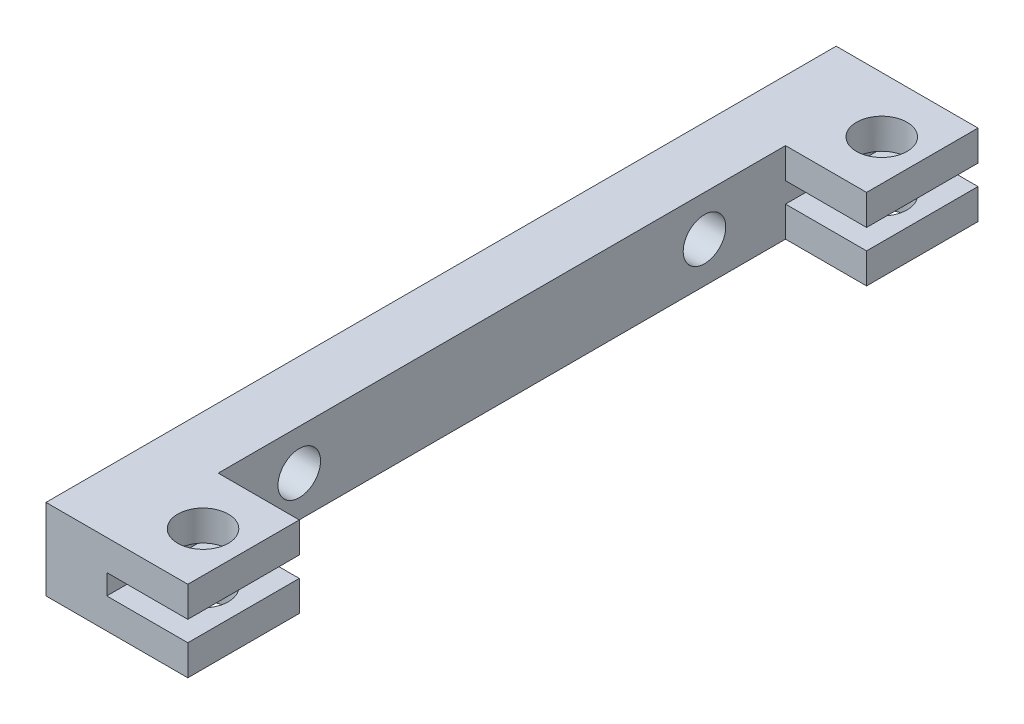
SolidWorks part; units mm, degrees
ref_plane "前视基准面" through (0, 0, 0) normal (0, 0, 1) x (1, 0, 0)
ref_plane "上视基准面" through (0, 0, 0) normal (0, 1, 0) x (1, 0, 0)
ref_plane "右视基准面" through (0, 0, 0) normal (1, 0, 0) x (0, 0, -1)
sketch "草图1" plane through (0, 0, 0) normal (0, 0, 1) x (1, 0, 0)
  line L0 (-5441.3907, 1449.7886) -> (-5441.3907, 1457.7886)
  line L1 (-5427.3907, 1457.7886) -> (-5427.3907, 1454.7886)
  line L2 (-5435.3907, 1454.7886) -> (-5435.3907, 1452.7886)
  line L3 (-5427.3907, 1452.7886) -> (-5427.3907, 1449.7886)
  line L4 (-5427.3907, 1449.7886) -> (-5441.3907, 1449.7886)
  line L5 (-5435.3907, 1454.7886) -> (-5427.3907, 1454.7886)
  line L6 (-5435.3907, 1452.7886) -> (-5427.3907, 1452.7886)
  line L7 (-5427.3907, 1457.7886) -> (-5441.3907, 1457.7886)
  line L20 (-5427.3907, 1453.7886) -> (-5441.3907, 1453.7886) construction
extrude "凸台-拉伸1" add sketch "草图1" along normal blind 78
sketch "草图2" plane through (0, 1457.7886, 0) normal (0, 1, 0) x (1, 0, 0)
  line L0 (-5441.3907, -39) -> (-5427.3907, -39) construction
  line L1 (-5441.3907, -78) -> (-5441.3907, 0) construction
  line L2 (-5427.3907, -78) -> (-5427.3907, 0) construction
  line L4 (-5427.3907, -67) -> (-5435.3907, -67)
  line L5 (-5427.3907, -67) -> (-5427.3907, -11)
  line L6 (-5427.3907, -11) -> (-5435.3907, -11)
  line L7 (-5435.3907, -67) -> (-5435.3907, -11)
  dimension "D1" = 56
  dimension "D2" = 8
extrude "切除-拉伸1" cut sketch "草图2" against normal through all
sketch "草图3" plane through (0, 1457.7886, 0) normal (0, 1, 0) x (1, 0, 0)
  line L0 (-5441.3907, -39) -> (-5421.4399, -39) construction
  line L1 (-5441.3907, -78) -> (-5441.3907, 0) construction
  circle A0 centre (-5431.3907, -72.5) radius 2.5
  circle A1 centre (-5431.3907, -5.5) radius 2.5
  dimension "D1" = 5
  dimension "D2" = 10
  dimension "D3" = 67
extrude "切除-拉伸2" cut sketch "草图3" against normal through all
hole_wizard "M5 螺纹孔1" positions "草图4" profile "草图5" tap size "M5" standard "ISO" end condition through all
sketch "草图4" plane through (-5441.3907, 0, 0) normal (-1, 0, 0) x (0, 0, 1)
  line L0 (39, 1449.7886) -> (39, 1457.7886) construction
  line L1 (78, 1449.7886) -> (0, 1449.7886) construction
  line L2 (78, 1457.7886) -> (0, 1457.7886) construction
  line L3 (39, 1457.7886) -> (39, 1453.7886) construction
  line L4 (39, 1453.7886) -> (30.7961, 1453.7886) construction
  point P0 (59, 1453.7886)
  point P2 (19, 1453.7886)
  point P16 (0, 0)
  point P17 (0, 0)
  dimension "D1" = 40
sketch "草图5" plane through (-5441.3907, 1453.7886, 59) normal (0, 1, 0) x (0, 0, 1)
  line L0 (0, 0) -> (0, 14)
  line L1 (0, 14) -> (2.1, 14)
  line L2 (2.1, 14) -> (2.1, 0)
  line L5 (2.1, 0) -> (0, 0)
  line L11 (0, -6.35) -> (0, 107.95) construction
  dimension "通孔螺纹孔钻头直径" = 4.2
  dimension "通孔螺纹孔钻头深度" = 14
cosmetic thread "孔螺蚊线1" parameters "D2"=5
cosmetic thread "孔螺蚊线2" parameters "D2"=5
